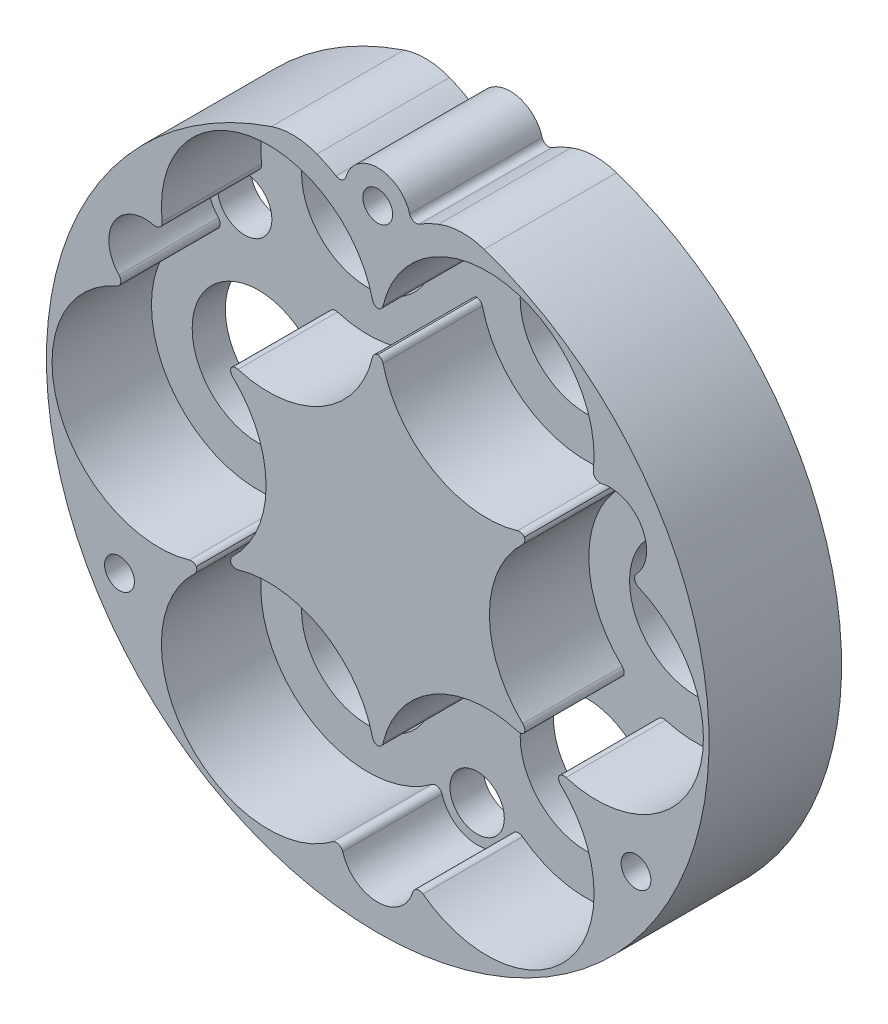
SolidWorks part; units mm, degrees
ref_plane "前视基准面" through (0, 0, 0) normal (0, 0, 1) x (1, 0, 0)
ref_plane "上视基准面" through (0, 0, 0) normal (0, 1, 0) x (1, 0, 0)
ref_plane "右视基准面" through (0, 0, 0) normal (1, 0, 0) x (0, 0, -1)
ref_plane "基准面4" through (0, 0, 0) normal (0, 0, -1) x (-1, 0, 0)
sketch "草图1" plane through (0, 0, 0) normal (0, 0, -1) x (-1, 0, 0)
  arc A0 (-163.0229, 198.2743) -> (-136.9771, 198.2743) centre (-150, 150) ccw
  arc A1 (-136.9771, 198.2743) -> (-143.7156, 195.773) centre (-133.5, 178.5788) ccw
  arc A2 (-143.7156, 195.773) -> (-145.1887, 196.3606) centre (-144.2264, 196.6328) cw
  arc A3 (-145.1887, 196.3606) -> (-154.8113, 196.3606) centre (-150, 195) ccw
  arc A4 (-154.8113, 196.3606) -> (-156.2844, 195.773) centre (-155.7736, 196.6328) cw
  arc A5 (-156.2844, 195.773) -> (-163.0229, 198.2743) centre (-166.5, 178.5788) ccw
extrude "凸台-拉伸1" add sketch "草图1" against normal blind 20
sketch "草图2" plane through (0, 0, 20) normal (0, 0, 1) x (1, 0, 0)
  arc A0 (189.3761, 164.838) -> (189.0484, 166.4481) centre (189.771, 165.7568) cw
  arc A1 (189.0484, 166.4481) -> (183.7686, 175.5928) centre (185.074, 170.25) ccw
  arc A2 (183.7686, 175.5928) -> (182.5382, 176.6817) centre (183.5313, 176.5643) cw
  arc A3 (182.5382, 176.6817) -> (150.7954, 182.3456) centre (166.5, 178.5788) ccw
  arc A4 (150.7954, 182.3456) -> (150, 181.5946) centre (149.823, 182.5788) cw
  arc A5 (150, 181.5946) -> (149.2046, 182.3456) centre (150.177, 182.5788) cw
  arc A6 (149.2046, 182.3456) -> (117.4618, 176.6817) centre (133.5, 178.5788) ccw
  arc A7 (117.4618, 176.6817) -> (116.2314, 175.5928) centre (116.4687, 176.5643) cw
  arc A8 (116.2314, 175.5928) -> (110.9516, 166.4481) centre (114.926, 170.25) ccw
  arc A9 (110.9516, 166.4481) -> (110.6239, 164.838) centre (110.229, 165.7568) cw
  arc A10 (110.6239, 164.838) -> (121.5902, 134.516) centre (117, 150) ccw
  arc A11 (121.5902, 134.516) -> (122.6382, 134.2027) centre (121.8744, 133.5573) cw
  arc A12 (122.6382, 134.2027) -> (122.3856, 133.1383) centre (121.6974, 133.8639) cw
  arc A13 (122.3856, 133.1383) -> (143.162, 108.4802) centre (133.5, 121.4212) ccw
  arc A14 (143.162, 108.4802) -> (144.7203, 107.9591) centre (143.7603, 107.6789) cw
  arc A15 (144.7203, 107.9591) -> (155.2797, 107.9591) centre (150, 109.5) ccw
  arc A16 (155.2797, 107.9591) -> (156.838, 108.4802) centre (156.2397, 107.6789) cw
  arc A17 (156.838, 108.4802) -> (177.6144, 133.1383) centre (166.5, 121.4212) ccw
  arc A18 (177.6144, 133.1383) -> (177.3618, 134.2027) centre (178.3026, 133.8639) cw
  arc A19 (177.3618, 134.2027) -> (178.4098, 134.516) centre (178.1256, 133.5573) cw
  arc A20 (178.4098, 134.516) -> (189.3761, 164.838) centre (183, 150) ccw
extrude "切除-拉伸1" cut sketch "草图2" against normal blind 15
sketch "草图3" plane through (0, 0, 5) normal (0, 0, 1) x (1, 0, 0)
  arc A0 (150.7954, 125.1879) -> (150, 124.437) centre (149.823, 125.4212) cw
  arc A1 (150, 124.437) -> (149.2046, 125.1879) centre (150.177, 125.4212) cw
  arc A2 (149.2046, 125.1879) -> (128.9098, 136.9051) centre (133.5, 121.4212) ccw
  arc A3 (128.9098, 136.9051) -> (127.8618, 137.2185) centre (128.6256, 137.8639) cw
  arc A4 (127.8618, 137.2185) -> (128.1144, 138.2828) centre (128.8026, 137.5573) cw
  arc A5 (128.1144, 138.2828) -> (128.1144, 161.7172) centre (117, 150) ccw
  arc A6 (128.1144, 161.7172) -> (127.8618, 162.7815) centre (128.8026, 162.4427) cw
  arc A7 (127.8618, 162.7815) -> (128.9098, 163.0949) centre (128.6256, 162.1361) cw
  arc A8 (128.9098, 163.0949) -> (149.2046, 174.8121) centre (133.5, 178.5788) ccw
  arc A9 (149.2046, 174.8121) -> (150, 175.563) centre (150.177, 174.5788) cw
  arc A10 (150, 175.563) -> (150.7954, 174.8121) centre (149.823, 174.5788) cw
  arc A11 (150.7954, 174.8121) -> (171.0902, 163.0949) centre (166.5, 178.5788) ccw
  arc A12 (171.0902, 163.0949) -> (172.1382, 162.7815) centre (171.3744, 162.1361) cw
  arc A13 (172.1382, 162.7815) -> (171.8856, 161.7172) centre (171.1974, 162.4427) cw
  arc A14 (171.8856, 161.7172) -> (171.8856, 138.2828) centre (183, 150) ccw
  arc A15 (171.8856, 138.2828) -> (172.1382, 137.2185) centre (171.1974, 137.5573) cw
  arc A16 (172.1382, 137.2185) -> (171.0902, 136.9051) centre (171.3744, 137.8639) cw
  arc A17 (171.0902, 136.9051) -> (150.7954, 125.1879) centre (166.5, 121.4212) ccw
extrude "凸台-拉伸2" add sketch "草图3" along normal blind 15
hole_wizard "Ø4.5 (4.5) 直径孔1" positions "草图5" profile "草图4" hole size "Ø4.5" standard "ANSI Metric"
sketch "草图5" plane through (0, 0, 0) normal (0, 0, -1) x (-1, 0, 0)
  point P0 (-150, 195)
  point P1 (-111.0289, 127.5)
  point P2 (-188.9711, 127.5)
sketch "草图4" plane through (150, 195, 0) normal (1, 0, 0) x (0, 1, 0)
  line L0 (0, 0) -> (0, 20)
  line L1 (0, 20) -> (2.25, 20)
  line L2 (2.25, 20) -> (2.25, 0)
  line L5 (2.25, 0) -> (0, 0)
  line L11 (0, -6.35) -> (0, 107.95) construction
  dimension "通孔孔直径" = 4.5
  dimension "通孔孔深度" = 20
hole_wizard "Ø20.0 (20) 直径孔1" positions "草图7" profile "草图6" hole size "Ø20.0" standard "ANSI Metric"
sketch "草图7" plane through (0, 0, 0) normal (0, 0, -1) x (-1, 0, 0)
  point P0 (-133.5, 178.5788)
  point P1 (-117, 150)
  point P2 (-133.5, 121.4212)
  point P3 (-166.5, 121.4212)
  point P4 (-183, 150)
  point P5 (-166.5, 178.5788)
sketch "草图6" plane through (133.5, 178.5788, 0) normal (1, 0, 0) x (0, 1, 0)
  line L0 (0, 0) -> (0, 20)
  line L1 (0, 20) -> (10, 20)
  line L2 (10, 20) -> (10, 0)
  line L5 (10, 0) -> (0, 0)
  line L11 (0, -6.35) -> (0, 107.95) construction
  dimension "通孔孔直径" = 20
  dimension "通孔孔深度" = 20
hole_wizard "Ø8.2 (8.2) 直径孔1" positions "草图9" profile "草图8" hole size "Ø8.2" standard "ANSI Metric"
sketch "草图9" plane through (0, 0, 0) normal (0, 0, -1) x (-1, 0, 0)
  point P0 (-114.926, 170.25)
  point P1 (-185.074, 170.25)
  point P2 (-150, 109.5)
sketch "草图8" plane through (114.926, 170.25, 0) normal (1, 0, 0) x (0, 1, 0)
  line L0 (0, 0) -> (0, 20)
  line L1 (0, 20) -> (4.1, 20)
  line L2 (4.1, 20) -> (4.1, 0)
  line L5 (4.1, 0) -> (0, 0)
  line L11 (0, -6.35) -> (0, 107.95) construction
  dimension "通孔孔直径" = 8.2
  dimension "通孔孔深度" = 20
fillet "圆角1" radius 10 2 edges at (163.0229, 198.2743, 10) (136.9771, 198.2743, 10)
